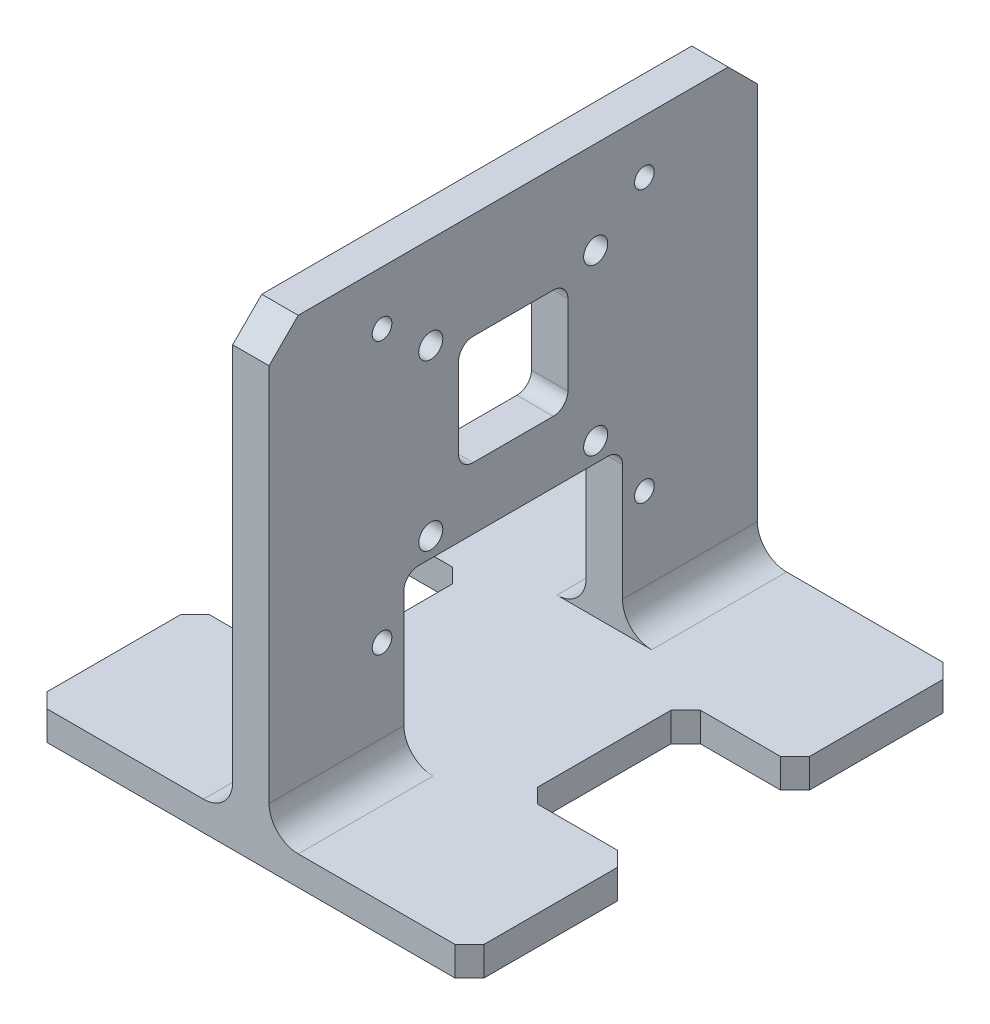
SolidWorks part; units mm, degrees
ref_plane "Front Plane" through (0, 0, 0) normal (0, 0, 1) x (1, 0, 0)
ref_plane "Top Plane" through (0, 0, 0) normal (0, 1, 0) x (1, 0, 0)
ref_plane "Right Plane" through (0, 0, 0) normal (1, 0, 0) x (0, 0, -1)
sketch "Sketch1" plane through (0, 0, 0) normal (0, 1, 0) x (1, 0, 0)
  line L0 (0, 55.4348) -> (0, -71.8696) construction
  line L1 (-30, 33.5) -> (30, 33.5)
  line L2 (30, 33.5) -> (30, 11.1667)
  line L3 (30, 11.1667) -> (15, 11.1667)
  line L4 (15, 11.1667) -> (15, -11.1667)
  line L5 (15, -11.1667) -> (30, -11.1667)
  line L6 (30, -11.1667) -> (30, -33.5)
  line L7 (30, -33.5) -> (-30, -33.5)
  line L8 (-30, -11.1667) -> (-30, -33.5)
  line L9 (-15, -11.1667) -> (-30, -11.1667)
  line L10 (-15, 11.1667) -> (-15, -11.1667)
  line L11 (-30, 11.1667) -> (-15, 11.1667)
  line L12 (-30, 33.5) -> (-30, 11.1667)
  point P12 (0, -33.5)
  point P17 (0, 33.5)
  dimension "D1" = 22.3333
  dimension "D2" = 30
  dimension "D3" = 15
  dimension "D4" = 22.3333
  dimension "D5" = 33.5
extrude "Boss-Extrude1" add sketch "Sketch1" along normal blind 4
sketch "Sketch2" plane through (0, 4, 0) normal (0, 1, 0) x (1, 0, 0)
  line L0 (-30, -33.5) -> (30, -33.5) construction
  line L1 (-2.5, 33.5) -> (2.5, 33.5)
  line L2 (-2.5, 33.5) -> (-2.5, -33.5)
  line L3 (-2.5, -33.5) -> (2.5, -33.5)
  line L4 (2.5, 33.5) -> (2.5, -33.5)
  line L5 (-2.5, 33.5) -> (2.5, -33.5) construction
  line L6 (-2.5, -33.5) -> (2.5, 33.5) construction
  point P0 (0, 0)
  dimension "D1" = 5
extrude "Boss-Extrude2" add sketch "Sketch2" along normal blind 60
sketch "Sketch3" plane through (-2.5, 0, 0) normal (-1, 0, 0) x (0, 0, 1)
  line L0 (-33.5, 4) -> (33.5, 4) construction
  line L1 (-11.315, 51.315) -> (11.315, 51.315) construction
  line L2 (-11.315, 51.315) -> (-11.315, 28.685) construction
  line L3 (-11.315, 28.685) -> (11.315, 28.685) construction
  line L4 (11.315, 51.315) -> (11.315, 28.685) construction
  line L5 (-11.315, 51.315) -> (11.315, 28.685) construction
  line L6 (-11.315, 28.685) -> (11.315, 51.315) construction
  line L12 (7.5, 47.5) -> (-7.5, 32.5) construction
  line L13 (7.5, 32.5) -> (-7.5, 47.5) construction
  circle A0 centre (-11.315, 51.315) radius 1.65
  circle A1 centre (-11.315, 28.685) radius 1.65
  circle A2 centre (11.315, 28.685) radius 1.65
  circle A3 centre (11.315, 51.315) radius 1.65
  point P0 (0, 40)
  point P12 (0, 40)
  point P17 (0, 0)
  dimension "D3" = 3.3
  dimension "D1" = 22.63
  dimension "D2" = 36
extrude "Cut-Extrude1" cut sketch "Sketch3" against normal through all
sketch "Sketch6" plane through (-2.5, 0, 0) normal (-1, 0, 0) x (0, 0, 1)
  line L0 (33.5, 4) -> (-33.5, 4) construction
  line L1 (-18, 56.64) -> (18, 56.64) construction
  line L2 (-18, 56.64) -> (-18, 19.36) construction
  line L3 (-18, 19.36) -> (18, 19.36) construction
  line L4 (18, 56.64) -> (18, 19.36) construction
  line L5 (-18, 56.64) -> (18, 19.36) construction
  line L6 (-18, 19.36) -> (18, 56.64) construction
  circle A0 centre (-18, 56.64) radius 1.35
  circle A1 centre (18, 56.64) radius 1.35
  circle A2 centre (18, 19.36) radius 1.35
  circle A3 centre (-18, 19.36) radius 1.35
  point P0 (0, 38)
  dimension "D3" = 2.7
  dimension "D1" = 36
  dimension "D2" = 37.28
  dimension "D4" = 34
extrude "Cut-Extrude3" cut sketch "Sketch6" against normal through all
sketch "Sketch8" plane through (2.5, 0, 0) normal (1, 0, 0) x (0, 0, -1)
  line L0 (-33.5, 4) -> (33.5, 4) construction
  line L1 (-7.5, 49.5) -> (7.5, 49.5)
  line L2 (-7.5, 49.5) -> (-7.5, 34.5)
  line L3 (-7.5, 34.5) -> (7.5, 34.5)
  line L4 (7.5, 49.5) -> (7.5, 34.5)
  line L5 (-7.5, 49.5) -> (7.5, 34.5) construction
  line L6 (-7.5, 34.5) -> (7.5, 49.5) construction
  point P0 (0, 42)
  point P5 (0, 0)
  dimension "D1" = 15
  dimension "D2" = 15
  dimension "D3" = 38
extrude "Cut-Extrude4" cut sketch "Sketch8" against normal through all
sketch "Sketch9" plane through (2.5, 0, 0) normal (1, 0, 0) x (0, 0, -1)
  line L0 (-33.5, 4) -> (33.5, 4) construction
  line L1 (-15, 26) -> (15, 26)
  line L2 (-15, 26) -> (-15, 4)
  line L3 (-15, 4) -> (15, 4)
  line L4 (15, 26) -> (15, 4)
  line L5 (-15, 26) -> (15, 4) construction
  line L6 (-15, 4) -> (15, 26) construction
  point P0 (0, 15)
  point P5 (0, 0)
  dimension "D1" = 30
  dimension "D2" = 22
  dimension "D3" = 0
extrude "Cut-Extrude5" cut sketch "Sketch9" against normal through all
fillet "Fillet1" radius 2 2 edges at (0, 26, 15) (0, 26, -15)
fillet "Fillet2" radius 2 4 edges at (0, 34.5, 7.5) (0, 49.5, 7.5) (0, 49.5, -7.5) (0, 34.5, -7.5)
chamfer "Chamfer1" distance 2 angle 45 8 edges at (30, 2, -33.5) (30, 2, 11.1667) (30, 2, -11.1667) (30, 2, 33.5) (-30, 2, 33.5) (-30, 2, 11.1667) (-30, 2, -33.5) (-30, 2, -11.1667)
chamfer "Chamfer2" distance 2 angle 45 4 edges at (15, 2, -11.1667) (15, 2, 11.1667) (-15, 2, 11.1667) (-15, 2, -11.1667)
chamfer "Chamfer3" distance 4 angle 45 2 edges at (0, 64, -33.5) (0, 64, 33.5)
fillet "Fillet4" radius 4 4 edges at (-2.5, 4, 24.25) (-2.5, 4, -24.25) (2.5, 4, -24.25) (2.5, 4, 24.25)
equation "\"D5@Sketch1\"=(\"D1@Sketch1\"+\"D4@Sketch1\"+\"D1@Sketch1\")/2"
